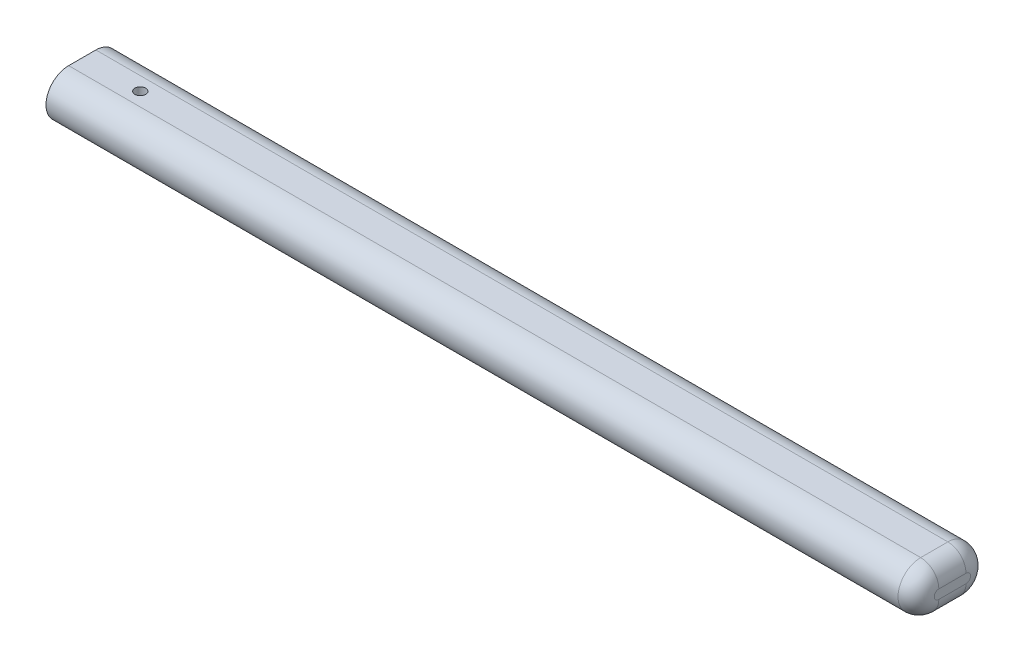
SolidWorks part; units mm, degrees
material "Balsa"
ref_plane "Alzado" through (0, 0, 0) normal (0, 0, 1) x (1, 0, 0)
ref_plane "Planta" through (0, 0, 0) normal (0, 1, 0) x (1, 0, 0)
ref_plane "Vista lateral" through (0, 0, 0) normal (1, 0, 0) x (0, 0, -1)
sketch "Croquis1" plane through (0, 0, 0) normal (1, 0, 0) x (0, 0, -1)
  line L0 (0, 0) -> (15, 0) construction
  line L1 (0, 12.5) -> (15, 12.5)
  line L2 (0, -12.5) -> (15, -12.5)
  arc A0 (0, 12.5) -> (0, -12.5) centre (0, 0) ccw
  arc A1 (15, -12.5) -> (15, 12.5) centre (15, 0) ccw
  point P3 (7.5, 0)
  dimension "D1" = 40
  dimension "D2" = 25
extrude "Saliente-Extruir1" add sketch "Croquis1" along normal blind 480
fillet "Redondeo1" radius 10 4 edges at (480, 12.5, -7.5) (480, 0, -27.5) (480, -12.5, -7.5) (480, 0, 12.5)
sketch "Croquis2" plane through (0, 12.5, 0) normal (0, 1, 0) x (1, 0, 0)
  line L1 (0, -12.5) -> (470, -12.5) construction
  line L2 (0, 15) -> (0, 0) construction
  circle A0 centre (32, 7.5) radius 3
  dimension "D2" = 6
  dimension "D1" = 20
  dimension "D3" = 32
extrude "Cortar-Extruir1" cut sketch "Croquis2" against normal up to surface (25 mm away) up to face at (235, -12.5, -7.5)
